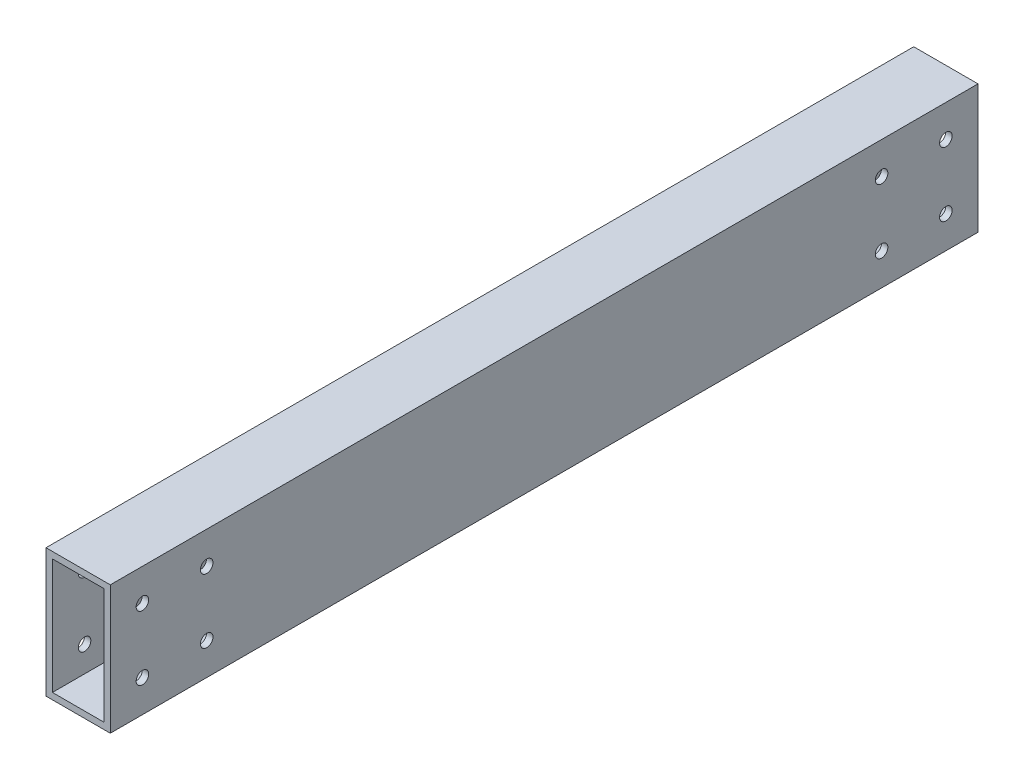
SolidWorks part; units mm, degrees
ref_plane "Front Plane" through (0, 0, 0) normal (0, 0, 1) x (1, 0, 0)
ref_plane "Top Plane" through (0, 0, 0) normal (0, 1, 0) x (1, 0, 0)
ref_plane "Right Plane" through (0, 0, 0) normal (1, 0, 0) x (0, 0, -1)
sketch "Sketch1" plane through (0, 0, 0) normal (0, 0, 1) x (1, 0, 0)
  line L1 (-12.7, -25.4) -> (12.7, -25.4)
  line L2 (-12.7, -25.4) -> (-12.7, 25.4)
  line L3 (-12.7, 25.4) -> (12.7, 25.4)
  line L4 (12.7, -25.4) -> (12.7, 25.4)
  line L5 (-12.7, -25.4) -> (12.7, 25.4) construction
  line L6 (-12.7, 25.4) -> (12.7, -25.4) construction
  point P0 (0, 0)
  dimension "D1" = 25.4
  dimension "D2" = 50.8
extrude "Extrude-Thin1" add sketch "Sketch1" against normal mid plane 342.9 thin thin type one direction reverse wall 2.54
sketch "Sketch2" plane through (0, 0, 0) normal (1, 0, 0) x (0, 0, -1)
  line L0 (171.45, 25.4) -> (171.45, -25.4) construction
  line L1 (158.75, -12.7) -> (133.35, -12.7) construction
  line L2 (158.75, -12.7) -> (158.75, 12.7) construction
  line L3 (158.75, 12.7) -> (133.35, 12.7) construction
  line L4 (133.35, -12.7) -> (133.35, 12.7) construction
  line L5 (158.75, -12.7) -> (133.35, 12.7) construction
  line L6 (158.75, 12.7) -> (133.35, -12.7) construction
  line L7 (-133.35, -12.7) -> (-158.75, -12.7) construction
  line L8 (-133.35, -12.7) -> (-133.35, 12.7) construction
  line L9 (-133.35, 12.7) -> (-158.75, 12.7) construction
  line L10 (-158.75, -12.7) -> (-158.75, 12.7) construction
  line L11 (-133.35, -12.7) -> (-158.75, 12.7) construction
  line L12 (-133.35, 12.7) -> (-158.75, -12.7) construction
  line L14 (-171.45, 25.4) -> (-171.45, -25.4) construction
  circle A0 centre (133.35, 12.7) radius 2.4765
  circle A1 centre (133.35, -12.7) radius 2.4765
  circle A2 centre (158.75, -12.7) radius 2.4765
  circle A3 centre (158.75, 12.7) radius 2.4765
  circle A4 centre (-133.35, 12.7) radius 2.4765
  circle A5 centre (-158.75, 12.7) radius 2.4765
  circle A6 centre (-158.75, -12.7) radius 2.4765
  circle A7 centre (-133.35, -12.7) radius 2.4765
  point P0 (146.05, 0)
  point P5 (-146.05, 0)
  dimension "D4" = 4.953
  dimension "D1" = 25.4
  dimension "D2" = 25.4
  dimension "D3" = 25.4
extrude "Cut-Extrude1" cut sketch "Sketch2" against normal through all both and the other way through all
